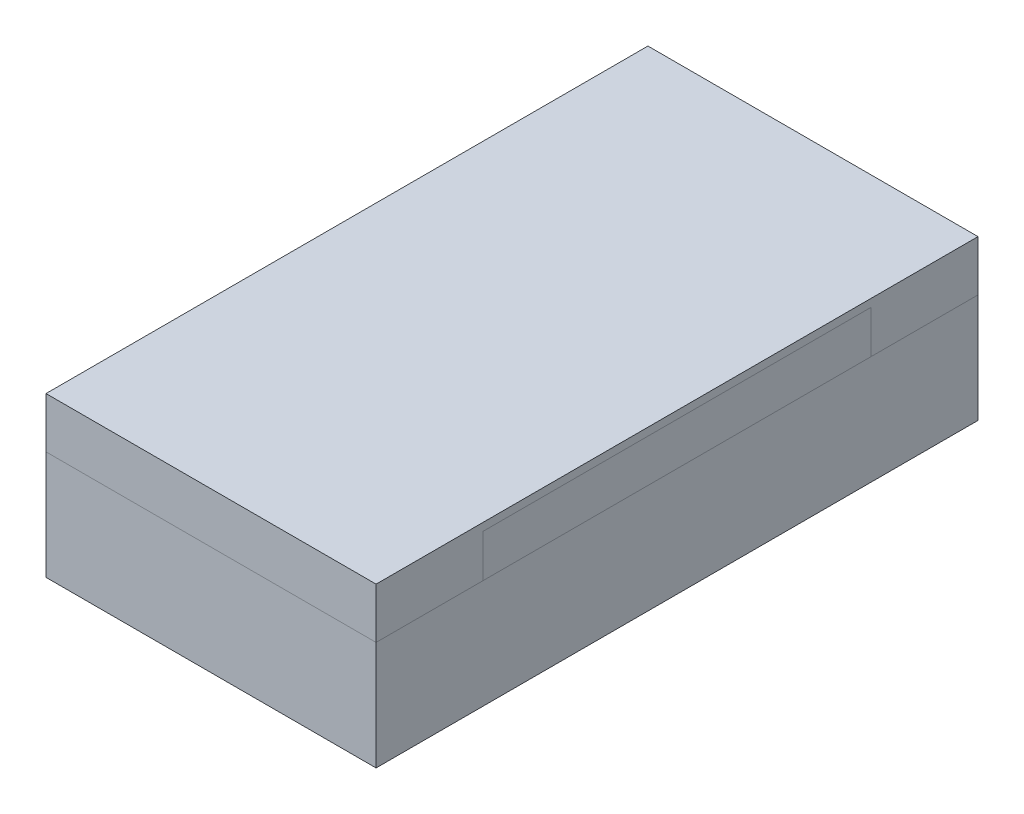
SolidWorks part; units mm, degrees
ref_plane "Front Plane" through (0, 0, 0) normal (0, 0, 1) x (1, 0, 0)
ref_plane "Top Plane" through (0, 0, 0) normal (0, 1, 0) x (1, 0, 0)
ref_plane "Right Plane" through (0, 0, 0) normal (1, 0, 0) x (0, 0, -1)
sketch "Sketch1" plane through (0, 0, 0) normal (0, 1, 0) x (1, 0, 0)
  line L1 (-0.425, -0.775) -> (0.425, -0.775)
  line L2 (-0.425, -0.775) -> (-0.425, 0.775)
  line L3 (-0.425, 0.775) -> (0.425, 0.775)
  line L4 (0.425, -0.775) -> (0.425, 0.775)
  line L5 (-0.425, -0.775) -> (0.425, 0.775) construction
  line L6 (-0.425, 0.775) -> (0.425, -0.775) construction
  point P0 (0, 0)
  dimension "D1" = 0.85
  dimension "D2" = 1.55
extrude "Boss-Extrude1" add sketch "Sketch1" along normal blind 0.28
sketch "Sketch2" plane through (0, 0.28, 0) normal (0, 1, 0) x (1, 0, 0)
  line L0 (-0.425, 0.775) -> (-0.425, -0.775) construction
  line L1 (0.425, 0.5) -> (-0.425, 0.5)
  line L2 (0.425, 0.5) -> (0.425, -0.5)
  line L3 (0.425, -0.5) -> (-0.425, -0.5)
  line L4 (-0.425, 0.5) -> (-0.425, -0.5)
  point P6 (-0.425, 0)
  point P7 (0, 0)
  point P9 (0.425, 0)
  point P11 (-0.425, 0)
  point P12 (0, 0)
  point P15 (0, 0)
  dimension "D1" = 1
extrude "Boss-Extrude2" add sketch "Sketch2" along normal blind 0.11 separate body
sketch "Sketch3" plane through (0, 0.39, 0) normal (0, 1, 0) x (1, 0, 0)
  line L1 (-0.425, 0.5) -> (0.425, 0.5)
  line L2 (-0.425, 0.5) -> (-0.425, -0.5)
  line L3 (-0.425, -0.5) -> (0.425, -0.5)
  line L4 (0.425, 0.5) -> (0.425, -0.5)
extrude "Boss-Extrude3" add sketch "Sketch3" along normal blind 0.02 separate body
sketch "Sketch4" plane through (0, 0.28, 0) normal (0, 1, 0) x (1, 0, 0)
  line L1 (0.425, 0.775) -> (-0.425, 0.775)
  line L2 (0.425, 0.775) -> (0.425, 0.5)
  line L3 (0.425, 0.5) -> (-0.425, 0.5)
  line L4 (-0.425, 0.775) -> (-0.425, 0.5)
  line L5 (0.425, -0.5) -> (-0.425, -0.5)
  line L6 (0.425, -0.5) -> (0.425, -0.775)
  line L7 (0.425, -0.775) -> (-0.425, -0.775)
  line L8 (-0.425, -0.5) -> (-0.425, -0.775)
extrude "Boss-Extrude5" add sketch "Sketch4" along normal up to surface (0.13 mm away) up to face at (0, 0.41, 0)
